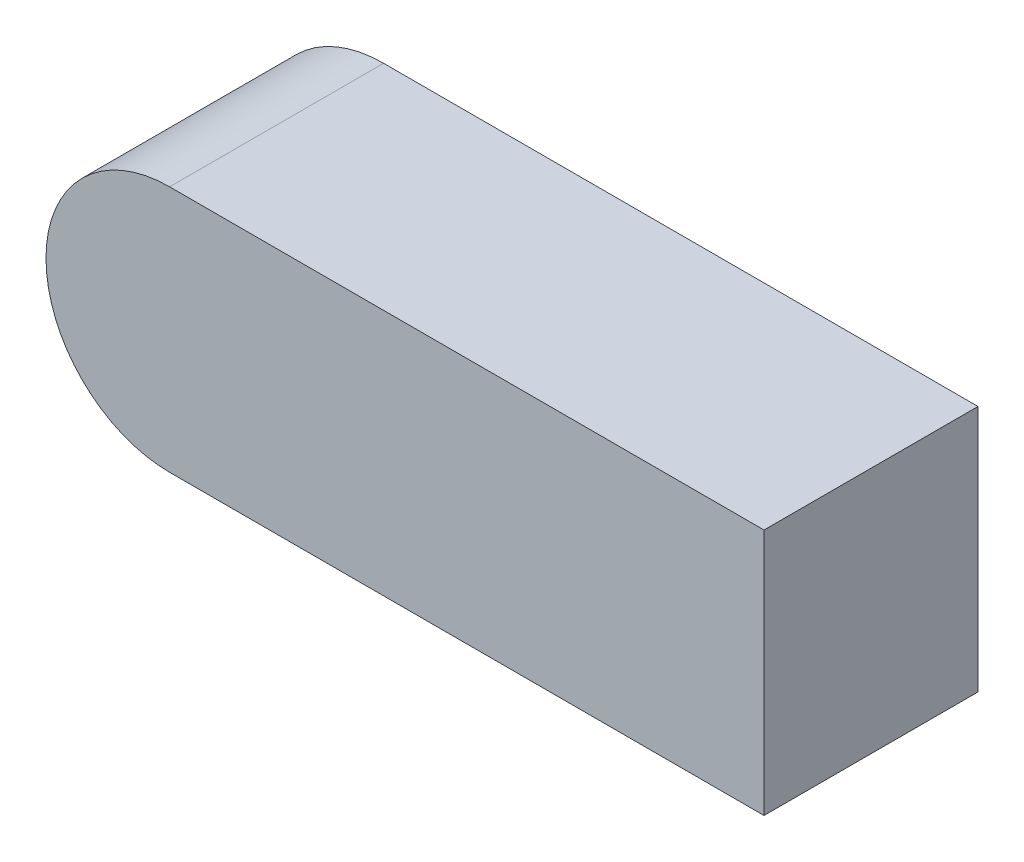
SolidWorks part; units mm, degrees
ref_plane "Front Plane" through (0, 0, 0) normal (0, 0, 1) x (1, 0, 0)
ref_plane "Top Plane" through (0, 0, 0) normal (0, 1, 0) x (1, 0, 0)
ref_plane "Right Plane" through (0, 0, 0) normal (1, 0, 0) x (0, 0, -1)
sketch "Sketch1" plane through (0, 0, 0) normal (1, 0, 0) x (0, 0, -1)
  line L1 (-22.5, -26) -> (22.5, -26)
  line L2 (-22.5, -26) -> (-22.5, 26)
  line L3 (-22.5, 26) -> (22.5, 26)
  line L4 (22.5, -26) -> (22.5, 26)
  line L5 (-22.5, -26) -> (22.5, 26) construction
  line L6 (-22.5, 26) -> (22.5, -26) construction
  point P0 (0, 0)
  dimension "D1" = 45
  dimension "D2" = 52
extrude "Boss-Extrude1" add sketch "Sketch1" along normal mid plane 125
sketch "Sketch3" plane through (0, 0, -22.5) normal (0, 0, -1) x (-1, 0, 0)
  line L0 (62.5, -26) -> (62.5, 26) construction
  line L1 (62.5, -26) -> (62.5, 26)
  arc A0 (62.5, -26) -> (62.5, 26) centre (62.5, 0) ccw
extrude "Boss-Extrude3" add sketch "Sketch3" against normal up to surface (45 mm away) up to face at (0, 0, 22.5)
